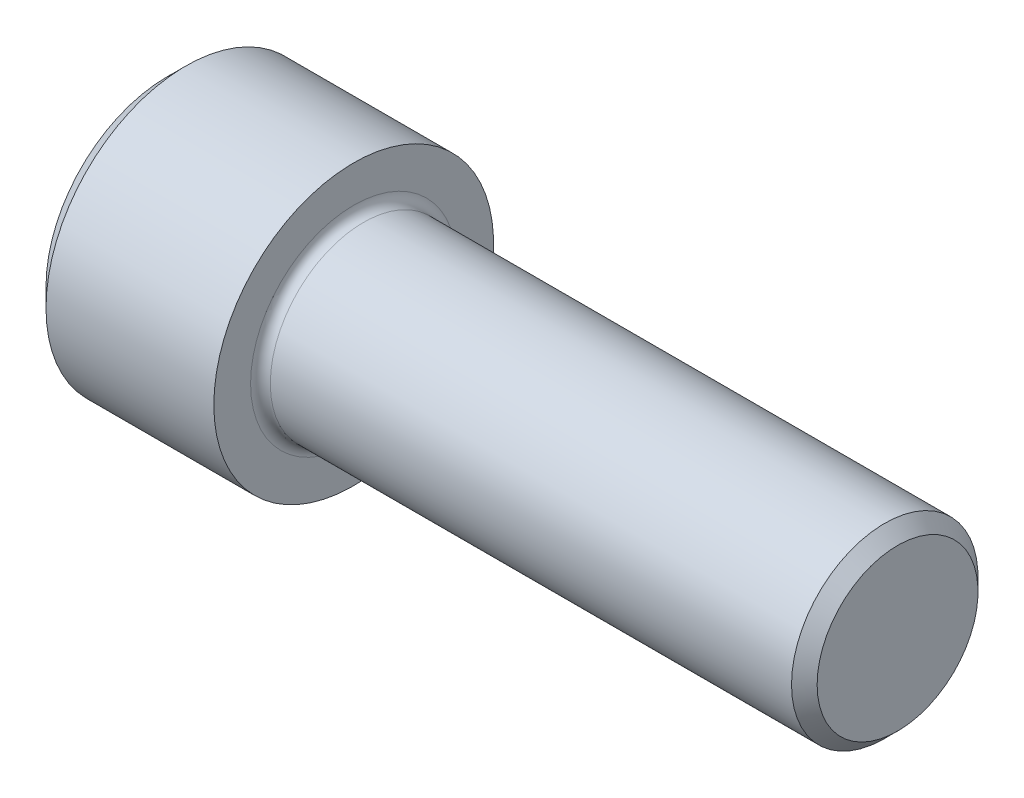
SolidWorks part; units mm, degrees
revolve "Base-Revolve" add sketch "BodySke"
sketch "BodySke" plane through (0, 0, 0) normal (0, 0, 1) x (1, 0, 0)
  line L0 (0, 0) -> (0, 15.6)
  line L1 (2.4, 18) -> (24, 18)
  line L2 (24, 18) -> (24, 12)
  line L3 (24, 12) -> (92.352, 12)
  line L4 (94, 10.352) -> (94, 0)
  line L5 (94, 0) -> (0, 0)
  line L6 (-31.75, 0) -> (127, 0) construction
  line L7 (0, 15.6) -> (2.4, 18)
  line L8 (94, 10.352) -> (92.352, 12)
  line L9 (0, -15.6) -> (2.4, -18) construction
  line L10 (94, -10.352) -> (92.352, -12) construction
  line L11 (27, 9.525) -> (27, 3.175) construction
  line L12 (44, 9.525) -> (44, 3.175) construction
  line L13 (44, 9.525) -> (44, 3.175) construction
  dimension "Diameter" = 24
  dimension "Head_ht" = 24
  dimension "Length" = 70
  dimension "Body_ch_ang" = 45
  dimension "Head_dia" = 36
  dimension "Head_ch_ang" = 45
  dimension "Minor_dia" = 20.704
  dimension "Advance" = 3
  dimension "Thread_nom" = 50
  dimension "Thread_length" = 50
  dimension "Head_ch_ht" = 2.4
cosmetic thread "ThreadCosmetic" [suppressed]
fillet "Fillet1" radius 1.27 1 edges at (24, 0, 12)
ref_plane "Plane1" through (0, 0, 0) normal (0, 0, 1) x (1, 0, 0)
ref_plane "Plane2" through (0, 0, 0) normal (0, 1, 0) x (1, 0, 0)
ref_plane "Plane3" through (0, 0, 0) normal (1, 0, 0) x (0, 0, -1)
other "Configuration Table"
sketch "Sketch2" plane through (0, 0, 0) normal (0, 0, 1) x (1, 0, 0)
  line L0 (0, 9.5) -> (12, 9.5)
  line L1 (12, 9.5) -> (17.4848, 0)
  line L2 (-31.75, 0) -> (127, 0) construction
  line L3 (17.4848, 0) -> (0, 0)
  line L4 (0, 0) -> (0, 9.5)
  line L5 (0, 15.6) -> (0, -15.6) construction
  line L6 (0, 0) -> (47.625, 0) construction
  line L7 (24, -18) -> (24, 18) construction
  dimension "D2" = 60
revolve "Hex-PreBroach" cut sketch "Sketch2" angle 360 about L6
sketch "Sketch3" plane through (0, 0, 0) normal (-1, 0, 0) x (0, 0.5, 0.866)
  line L0 (5.4848, 9.5) -> (-5.4848, 9.5)
  line L1 (-5.4848, 9.5) -> (-10.9697, 0)
  line L2 (5.4848, 9.5) -> (10.9697, 0)
  line L3 (5.4848, -9.5) -> (10.9697, 0)
  line L4 (5.4848, -9.5) -> (-5.4848, -9.5)
  line L5 (-5.4848, -9.5) -> (-10.9697, 0)
extrude "Hex" cut sketch "Sketch3" against normal blind 12
sketch "Sketch4" plane through (0, 0, 0) normal (-1, 0, 0) x (0, 0, 1)
  line L0 (0, 0) -> (10.1727, 0)
  line L1 (0, 0) -> (6.1484, 3.5498) construction
  line L2 (0, 0) -> (5.0863, 8.8098)
  line L3 (8.4417, 2.1022) -> (9.7612, 2.864)
  line L4 (6.0414, 6.2596) -> (7.3609, 7.0215)
  arc A0 (8.4417, 2.1022) -> (6.0414, 6.2596) centre (0, 0) ccw
  arc A1 (10.1727, 0) -> (9.7612, 2.864) centre (0, 0) ccw
  arc A2 (5.0863, 8.8098) -> (7.3609, 7.0215) centre (0, 0) cw
  dimension "D1" = 30
  dimension "D2" = 60
extrude "Spline" [suppressed] cut sketch "Sketch4" against normal blind 12.573
pattern_circular "CirPattern1" [suppressed] count 6 every 60
sketch "Sketch5" plane through (0, 0, 0) normal (0, 0, 1) x (1, 0, 0)
  line L0 (-31.75, 0) -> (127, 0) construction
  line L2 (0, 15.6) -> (0, -15.6) construction
  circle A0 centre (7.3, 0) radius 1.075
  dimension "Drilled_hole_dia" = 2.15
  dimension "Drilled_hole_loc" = 7.3
extrude "Hole" [suppressed] cut sketch "Sketch5" against normal through all and the other way through all
pattern_circular "Drilled-4" [suppressed] count 2 every 60
pattern_circular "Drilled-6" [suppressed] count 3 every 60
sketch "ThdSchSke" plane through (0, 0, 0) normal (0, 0, 1) x (1, 0, 0)
  line L0 (44, -10.352) -> (42.8461, -12)
  line L1 (44, -10.352) -> (45.1539, -12)
  line L2 (45.1539, -12) -> (45.1539, -15)
  line L3 (-3.175, 0) -> (5.1513, 0) construction
  line L5 (45.1539, -15) -> (42.8461, -15)
  line L6 (42.8461, -15) -> (42.8461, -12)
  line L7 (0, 15.6) -> (0, -15.6) construction
revolve "ThreadSchematic" [suppressed] cut sketch "ThdSchSke" angle 360 about L3
pattern_linear "ThdSchPat" [suppressed]
equation "\"D2@Sketch3\" = \"Hex_size@Sketch3\" / 2"
equation "\"D1@Sketch3\" = \"Hex_size@Sketch3\" / 2"
equation "\"D1@Sketch2\" = \"Hex_size@Sketch3\" / 2"
equation "\"D3@Sketch4\" = \"Spline_p_dim@Sketch4\" / 2"
equation "\"Thread_minor@ThreadCosmetic\"  =  \"Minor_dia@BodySke\""
equation "\"D2@CirPattern1\" = 360 / \"Num_teeth@CirPattern1\""
equation "\"Wall_thickness@Sketch2\" = \"Head_ht@BodySke\" - \"Key_eng@Hex\""
equation "\"Thread_length@ThreadCosmetic\" = ((sgn( (\"Length@BodySke\" - \"Advance@BodySke\" ) - \"Thread_nom@BodySke\" )-1)*( (\"Length@BodySke\" - \"Advance@BodySke\" ) - \"Thread_nom@BodySke\" ))/-2+ \"Thread_nom@BodySke\""
equation "\"Thread_minor@ThdSchSke\" = \"Minor_dia@BodySke\""
equation "\"Diameter@ThdSchSke\" = \"Diameter@BodySke\""
equation "\"Overcut@ThdSchSke\" = \"Diameter@BodySke\" * 1.25"
equation "\"Start@ThdSchSke\" = \"Head_ht@BodySke\" + \"Length@BodySke\" - \"Thread_length@ThreadCosmetic\"  '---Non-countersunk---"
equation "\"Num_threads@ThdSchPat\" = int( \"Thread_length@ThreadCosmetic\" / \"Advance@BodySke\" + 0.999 )  + 1"
equation "\"Advance@ThdSchPat\" = \"Thread_length@ThreadCosmetic\" /  (\"Num_threads@ThdSchPat\" - 1) 'relax it"
equation "\"Num_threads@ThdSchPat\" = \"Num_threads@ThdSchPat\" - sgn( \"Num_threads@ThdSchPat\" - 1) '---chamfered tips only---"
